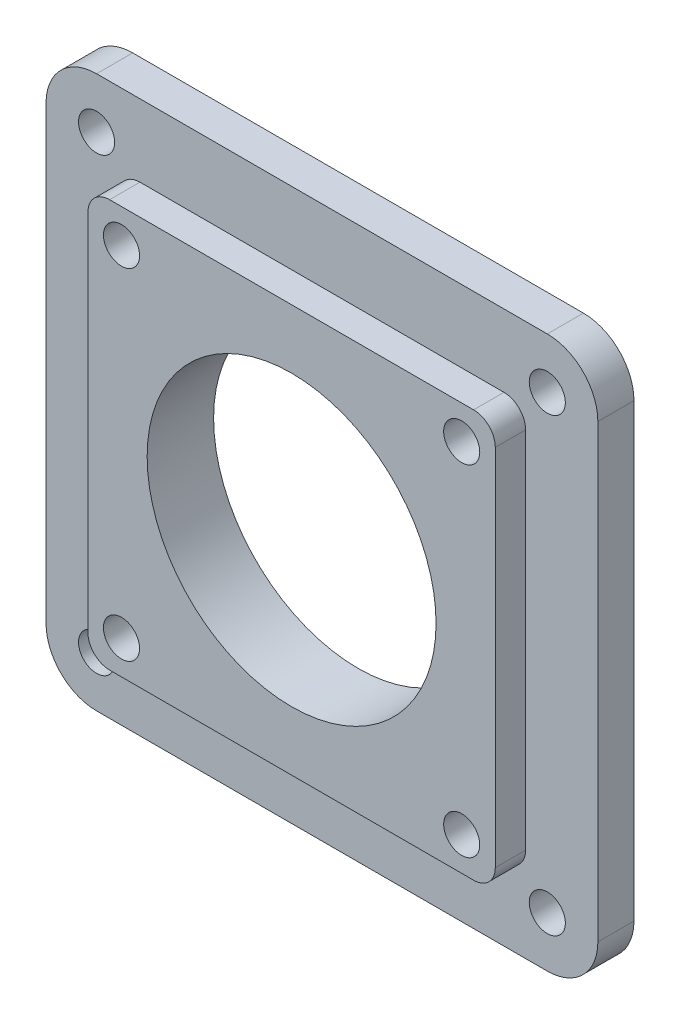
SolidWorks part; units mm, degrees
ref_plane "Front Plane" through (0, 0, 0) normal (0, 0, 1) x (1, 0, 0)
ref_plane "Top Plane" through (0, 0, 0) normal (0, 1, 0) x (1, 0, 0)
ref_plane "Right Plane" through (0, 0, 0) normal (1, 0, 0) x (0, 0, -1)
sketch "Sketch1" plane through (0, 0, 0) normal (0, 0, 1) x (1, 0, 0)
  line L1 (-28.2, -28.2) -> (28.2, -28.2)
  line L2 (-28.2, -28.2) -> (-28.2, 28.2)
  line L3 (-28.2, 28.2) -> (28.2, 28.2)
  line L4 (28.2, -28.2) -> (28.2, 28.2)
  line L5 (-28.2, -28.2) -> (28.2, 28.2) construction
  line L6 (-28.2, 28.2) -> (28.2, -28.2) construction
  point P0 (0, 0)
  dimension "D1" = 56.4
  dimension "D2" = 56.4
extrude "Boss-Extrude1" add sketch "Sketch1" along normal blind 4.2
sketch "Sketch2" plane through (0, 0, 4.2) normal (0, 0, 1) x (1, 0, 0)
  line L0 (-28.2, 0) -> (0, 0) construction
  line L1 (-28.2, 28.2) -> (-28.2, -28.2) construction
  circle A0 centre (0, 0) radius 19.15
  dimension "D1" = 38.3
extrude "Cut-Extrude1" cut sketch "Sketch2" against normal blind 1.6
sketch "Sketch4" plane through (0, 0, 0) normal (0, 0, -1) x (-1, 0, 0)
  line L0 (-28.2, -28.2) -> (-28.2, 28.2) construction
  line L1 (38.2, -38.2) -> (-38.2, -38.2)
  line L2 (38.2, -38.2) -> (38.2, 38.2)
  line L3 (38.2, 38.2) -> (-38.2, 38.2)
  line L4 (-38.2, -38.2) -> (-38.2, 38.2)
  line L5 (38.2, -38.2) -> (-38.2, 38.2) construction
  line L6 (38.2, 38.2) -> (-38.2, -38.2) construction
  line L7 (28.2, -28.2) -> (-28.2, -28.2) construction
  point P0 (0, 0)
  dimension "D1" = 10
  dimension "D2" = 10
extrude "Boss-Extrude2" add sketch "Sketch4" along normal blind 5
sketch "Sketch3" plane through (0, 0, 2.6) normal (0, 0, 1) x (1, 0, 0)
  line L1 (23.55, 23.55) -> (-23.55, 23.55) construction
  line L2 (23.55, 23.55) -> (23.55, -23.55) construction
  line L3 (23.55, -23.55) -> (-23.55, -23.55) construction
  line L4 (-23.55, 23.55) -> (-23.55, -23.55) construction
  line L5 (23.55, 23.55) -> (-23.55, -23.55) construction
  line L6 (23.55, -23.55) -> (-23.55, 23.55) construction
  circle A0 centre (0, 0) radius 10
  circle A1 centre (23.55, -23.55) radius 2.5
  circle A2 centre (-23.55, -23.55) radius 2.5
  circle A3 centre (-23.55, 23.55) radius 2.5
  circle A4 centre (23.55, 23.55) radius 2.5
  dimension "D1" = 20
  dimension "D2" = 47.1
  dimension "D3" = 47.1
extrude "Cut-Extrude2" cut sketch "Sketch3" against normal through all both and the other way through all contours A0 | A1 | A2 | A3 | A4
sketch "Sketch5" plane through (0, 0, -5) normal (0, 0, -1) x (-1, 0, 0)
  line L0 (-38.2, 38.2) -> (-38.2, -38.2) construction
  line L1 (31.2, -31.2) -> (-31.2, -31.2) construction
  line L2 (31.2, -31.2) -> (31.2, 31.2) construction
  line L3 (31.2, 31.2) -> (-31.2, 31.2) construction
  line L4 (-31.2, -31.2) -> (-31.2, 31.2) construction
  line L5 (31.2, -31.2) -> (-31.2, 31.2) construction
  line L6 (31.2, 31.2) -> (-31.2, -31.2) construction
  line L7 (-38.2, -38.2) -> (38.2, -38.2) construction
  circle A0 centre (-31.2, -31.2) radius 2.5
  circle A1 centre (-31.2, 31.2) radius 2.5
  circle A2 centre (31.2, 31.2) radius 2.5
  circle A3 centre (31.2, -31.2) radius 2.5
  point P0 (0, 0)
  point P20 (0, 0)
  dimension "D3" = 4
  dimension "D1" = 7
  dimension "D2" = 7
fillet "Fillet1" radius 7 4 edges at (-38.2, -38.2, -2.5) (-38.2, 38.2, -2.5) (38.2, 38.2, -2.5) (38.2, -38.2, -2.5)
fillet "Fillet2" radius 3 4 edges at (28.2, -28.2, 2.1) (28.2, 28.2, 2.1) (-28.2, -28.2, 2.1) (-28.2, 28.2, 2.1)
extrude "Cut-Extrude4" cut sketch "Sketch5" against normal blind 10
sketch "Sketch6" plane through (0, 0, -5) normal (0, 0, -1) x (-1, 0, 0)
  circle A0 centre (0, 0) radius 20
  dimension "D1" = 40
extrude "Cut-Extrude5" cut sketch "Sketch6" against normal blind 10
